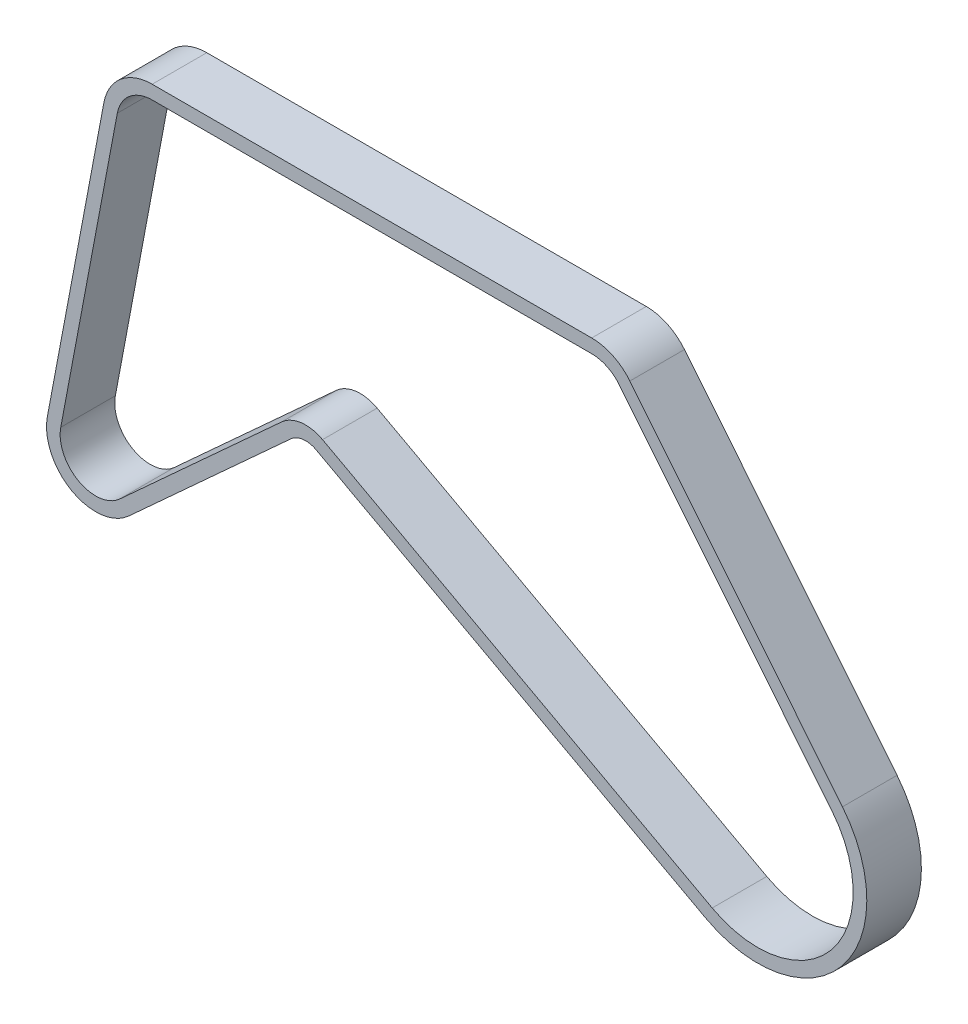
SolidWorks part; units mm, degrees
ref_plane "Front Plane" through (0, 0, 0) normal (0, 0, 1) x (1, 0, 0)
ref_plane "Top Plane" through (0, 0, 0) normal (0, 1, 0) x (1, 0, 0)
ref_plane "Right Plane" through (0, 0, 0) normal (1, 0, 0) x (0, 0, -1)
sketch "Sketch2" plane through (0, 0, 0) normal (0, 0, 1) x (1, 0, 0)
  line L0 (0, 0) -> (1, 0) construction
  line L1 (0, 0) -> (0, 1) construction
  line L2 (27.1965, 22.0307) -> (-50.6922, 118.1828)
  line L3 (-60.7937, 123) -> (-221.8191, 123)
  line L4 (-234.5945, 112.4059) -> (-255.3096, 2.4059)
  line L5 (-233.773, -9.6042) -> (-174.3489, 44.6042)
  line L6 (-159.4024, 46.4343) -> (-16.6526, -30.7846)
  arc A0 (-16.6526, -30.7846) -> (27.1965, 22.0307) centre (0, 0) ccw
  arc A1 (-50.6922, 118.1828) -> (-60.7937, 123) centre (-60.7937, 110) ccw
  arc A2 (-221.8191, 123) -> (-234.5945, 112.4059) centre (-221.8191, 110) ccw
  arc A3 (-255.3096, 2.4059) -> (-233.773, -9.6042) centre (-242.5342, 0) ccw
  arc A4 (-174.3489, 44.6042) -> (-159.4024, 46.4343) centre (-165.5877, 35) cw
extrude "Extrude-Thin1" add sketch "Sketch2" along normal mid plane 20 thin
